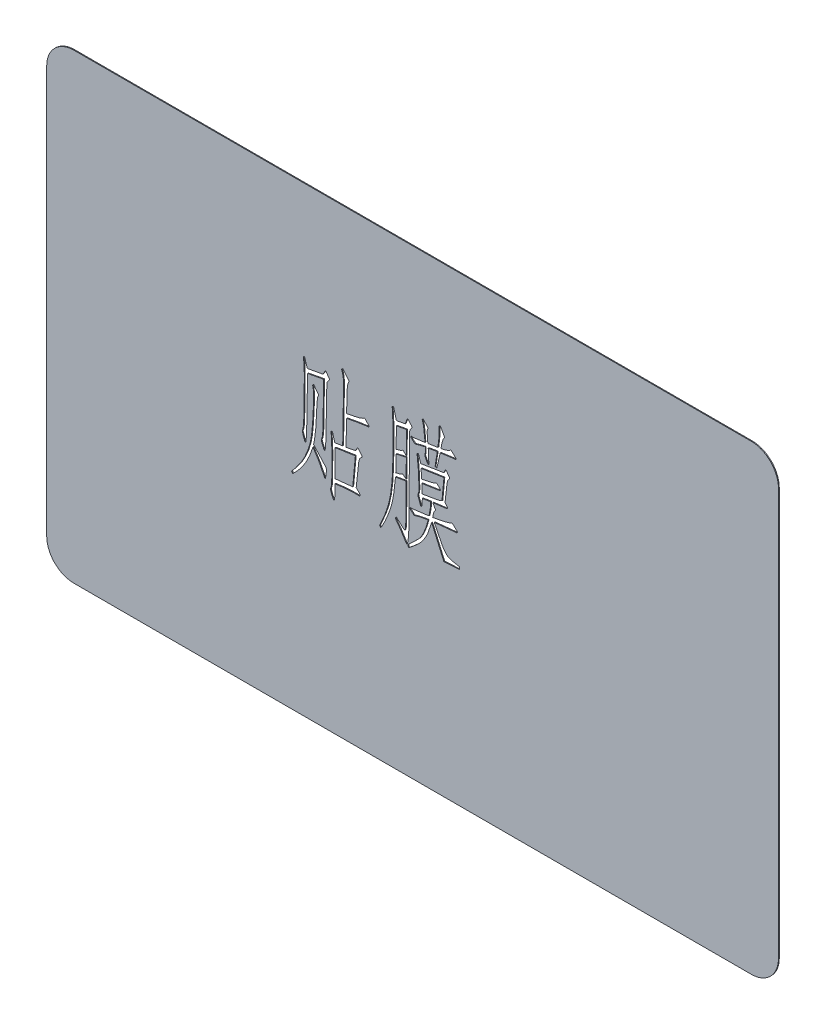
SolidWorks part; units mm, degrees
ref_plane "前视基准面" through (0, 0, 0) normal (0, 0, 1) x (1, 0, 0)
ref_plane "上视基准面" through (0, 0, 0) normal (0, 1, 0) x (1, 0, 0)
ref_plane "右视基准面" through (0, 0, 0) normal (1, 0, 0) x (0, 0, -1)
sketch "草图1" plane through (0, 0, 0) normal (0, 0, 1) x (1, 0, 0)
  line L1 (0, 0) -> (85.6, 0)
  line L2 (0, 0) -> (0, 54)
  line L3 (0, 54) -> (85.6, 54)
  line L4 (85.6, 0) -> (85.6, 54)
  dimension "D1" = 85.6
  dimension "D2" = 54
extrude "凸台-拉伸1" add sketch "草图1" along normal blind 0.1
sketch "草图2" plane through (0, 0, 0.1) normal (0, 0, 1) x (1, 0, 0)
  text T0 "贴膜" font "汉仪长仿宋体" height 10
extrude "切除-拉伸1" cut sketch "草图2" against normal blind 0.1
fillet "圆角1" radius 3.18 4 edges at (85.6, 0, 0.05) (85.6, 54, 0.05) (0, 0, 0.05) (0, 54, 0.05)
